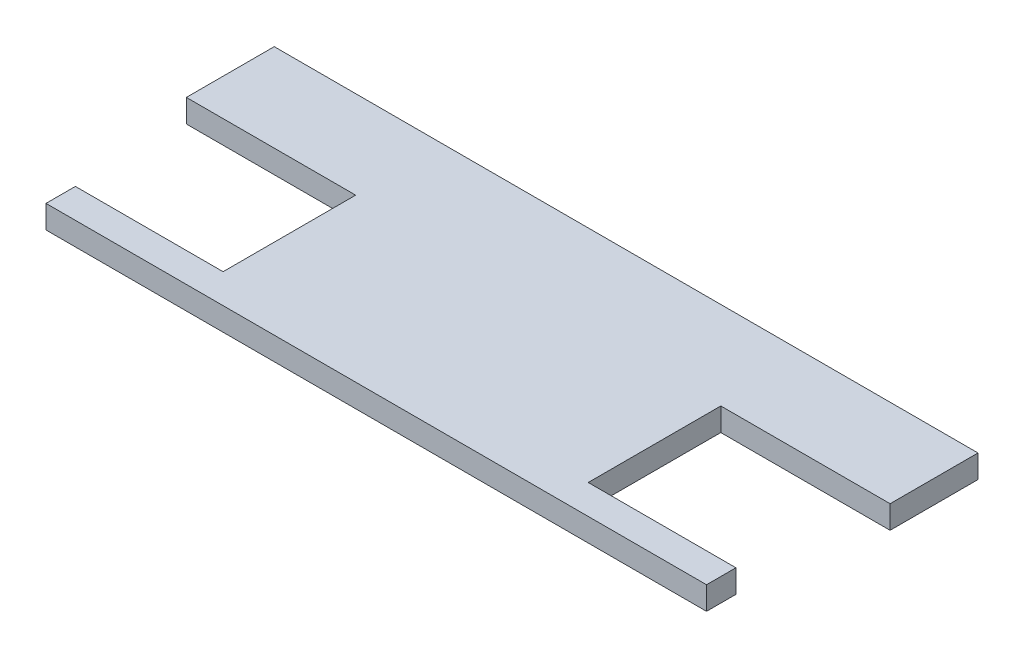
SolidWorks part; units mm, degrees
ref_plane "Front Plane" through (0, 0, 0) normal (0, 0, 1) x (1, 0, 0)
ref_plane "Top Plane" through (0, 0, 0) normal (0, 1, 0) x (1, 0, 0)
ref_plane "Right Plane" through (0, 0, 0) normal (1, 0, 0) x (0, 0, -1)
sketch "Sketch1" plane through (0, 0, 0) normal (0, 1, 0) x (1, 0, 0)
  line L1 (0, 0) -> (48.84, 0)
  line L2 (0, 0) -> (0, 17.34)
  line L3 (0, 17.34) -> (48.84, 17.34)
  line L4 (48.84, 0) -> (48.84, 17.34)
  dimension "D1" = 48.84
  dimension "D2" = 17.34
extrude "main square" add sketch "Sketch1" along normal blind 1.6
sketch "Sketch2" plane through (0, 1.6, 0) normal (0, 1, 0) x (1, 0, 0)
  line L0 (0, 17.34) -> (0, 0) construction
  line L2 (0, 11.24) -> (11.75, 11.24)
  line L3 (0, 11.24) -> (0, 2.04)
  line L5 (0, 2.04) -> (11.75, 2.04)
  line L6 (11.75, 11.24) -> (11.75, 2.04)
  line L7 (48.84, 17.34) -> (0, 17.34) construction
  line L10 (24.42, 17.34) -> (24.42, 0) construction
  line L11 (1.5, 2.04) -> (0, 2.04)
  line L12 (1.5, 2.04) -> (1.5, 0)
  line L14 (1.5, 0) -> (0, 0)
  line L15 (0, 2.04) -> (0, 0)
  line L16 (0, 0) -> (48.84, 0) construction
  dimension "D1" = 9.2
  dimension "D2" = 6.1
  dimension "D3" = 11.75
  dimension "D4" = 1.5
extrude "servo holes" cut sketch "Sketch2" against normal blind 1.6
ref_plane "Plane1" through (24.42, 0, 0) normal (-1, 0, 0) x (0, 0, 1)
mirror "Mirror1" about plane through (24.42, 0, 0) normal (-1, 0, 0) of "servo holes"
sketch "switch location" plane through (0, 1.6, 0) normal (0, 1, 0) x (1, 0, 0)
  line L1 (0, 17.34) -> (0, 11.24) construction
  line L3 (20.15, 9.75) -> (29.05, 9.75)
  line L4 (20.15, 9.75) -> (20.15, 6.1)
  line L5 (20.15, 6.1) -> (29.05, 6.1)
  line L6 (29.05, 9.75) -> (29.05, 6.1)
  line L7 (24.6, 9.75) -> (24.6, 6.1) construction
  line L8 (20.15, 7.925) -> (29.05, 7.925) construction
  line L9 (1.5, 0) -> (47.34, 0) construction
  dimension "D1" = 24.6
  dimension "D2" = 6.1
  dimension "D3" = 3.65
  dimension "D4" = 8.9
